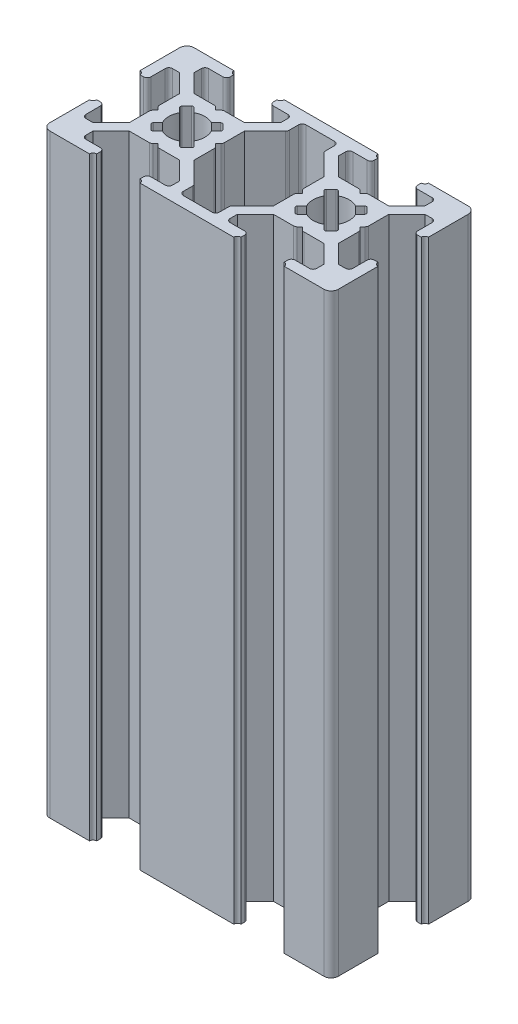
SolidWorks part; units mm, degrees
ref_plane "Front Plane" through (0, 0, 0) normal (0, 0, 1) x (1, 0, 0)
ref_plane "Top Plane" through (0, 0, 0) normal (0, 1, 0) x (1, 0, 0)
ref_plane "Right Plane" through (0, 0, 0) normal (1, 0, 0) x (0, 0, -1)
sketch "Sketch2" plane through (0, 0, 0) normal (0, 1, 0) x (1, 0, 0)
  line L0 (0, 13) -> (1.5, 13)
  line L1 (0, 0) -> (40, 0)
  line L2 (0, 0) -> (0, 20)
  line L3 (0, 20) -> (40, 20)
  line L4 (40, 0) -> (40, 20)
  line L9 (5.5, 6.5) -> (3, 4)
  line L10 (3, 4) -> (1.5, 4)
  line L11 (1.5, 4) -> (1.5, 7)
  line L12 (1.5, 7) -> (0, 7)
  line L13 (0, 7) -> (0, 13)
  line L14 (1.5, 13) -> (1.5, 16)
  line L15 (1.5, 16) -> (3, 16)
  line L16 (3, 16) -> (5.5, 13.5)
  line L17 (5.5, 10.5) -> (6, 10)
  line L18 (6, 10) -> (5.5, 9.5)
  line L19 (5.5, 9.5) -> (5.5, 10.5)
  line L20 (20, 20) -> (20, 0) construction
  line L31 (7, 18.5) -> (7, 20)
  line L32 (7, 18.5) -> (4, 18.5)
  line L33 (4, 18.5) -> (4, 17)
  line L34 (4, 17) -> (6.5, 14.5)
  line L38 (16, 18.5) -> (13, 18.5)
  line L39 (13, 18.5) -> (13, 20)
  line L40 (7, 20) -> (13, 20)
  line L41 (16, 18.5) -> (16, 17)
  line L42 (16, 17) -> (13.5, 14.5)
  line L53 (0, 10) -> (40, 10) construction
  line L89 (17.5, 18.5) -> (22.5, 18.5)
  line L90 (22.5, 18.5) -> (22.5, 16.5)
  line L91 (22.5, 16.5) -> (25.5, 13.5)
  line L92 (25.5, 13.5) -> (25.5, 6.5)
  line L93 (25.5, 6.5) -> (22.5, 3.5)
  line L94 (22.5, 3.5) -> (22.5, 1.5)
  line L95 (22.5, 1.5) -> (17.5, 1.5)
  line L96 (17.5, 1.5) -> (17.5, 3.5)
  line L97 (17.5, 3.5) -> (14.5, 6.5)
  line L98 (14.5, 6.5) -> (14.5, 13.5)
  line L99 (14.5, 13.5) -> (17.5, 16.5)
  line L100 (17.5, 16.5) -> (17.5, 18.5)
  line L102 (5.5, 13.5) -> (5.5, 10)
  line L103 (5.5, 10) -> (5.5, 6.5)
  line L104 (13.5, 14.5) -> (10, 14.5)
  line L105 (10, 14.5) -> (6.5, 14.5)
  line L106 (14.5, 10.5) -> (14.5, 9.5)
  line L107 (14.5, 9.5) -> (14, 10)
  line L108 (14, 10) -> (14.5, 10.5)
  line L109 (7, 18.5) -> (13, 18.5) construction
  line L110 (9.5, 14.5) -> (10.5, 14.5)
  line L111 (10.5, 14.5) -> (10, 14)
  line L112 (10, 14) -> (9.5, 14.5)
  line L113 (10.5, 5.5) -> (10, 6)
  line L114 (9.5, 5.5) -> (10.5, 5.5)
  line L115 (10, 6) -> (9.5, 5.5)
  line L116 (13.5, 5.5) -> (10, 5.5)
  line L117 (16, 3) -> (13.5, 5.5)
  line L118 (16, 1.5) -> (16, 3)
  line L119 (16, 1.5) -> (13, 1.5)
  line L120 (13, 1.5) -> (13, 0)
  line L121 (7, 0) -> (13, 0)
  line L122 (7, 1.5) -> (7, 0)
  line L123 (7, 1.5) -> (4, 1.5)
  line L124 (4, 1.5) -> (4, 3)
  line L125 (4, 3) -> (6.5, 5.5)
  line L126 (10, 5.5) -> (6.5, 5.5)
  line L127 (30.5, 5.5) -> (29.5, 5.5)
  line L128 (30, 6) -> (30.5, 5.5)
  line L129 (29.5, 5.5) -> (30, 6)
  line L130 (24, 3) -> (26.5, 5.5)
  line L131 (24, 1.5) -> (24, 3)
  line L132 (24, 1.5) -> (27, 1.5)
  line L133 (27, 1.5) -> (27, 0)
  line L134 (33, 0) -> (27, 0)
  line L135 (33, 1.5) -> (33, 0)
  line L136 (33, 1.5) -> (36, 1.5)
  line L137 (36, 1.5) -> (36, 3)
  line L138 (36, 3) -> (33.5, 5.5)
  line L139 (30, 5.5) -> (33.5, 5.5)
  line L140 (26.5, 5.5) -> (30, 5.5)
  line L141 (34, 10) -> (34.5, 9.5)
  line L142 (34.5, 10.5) -> (34, 10)
  line L143 (34.5, 9.5) -> (34.5, 10.5)
  line L144 (34.5, 13.5) -> (34.5, 10)
  line L145 (37, 16) -> (34.5, 13.5)
  line L146 (38.5, 16) -> (37, 16)
  line L147 (38.5, 13) -> (38.5, 16)
  line L148 (40, 13) -> (38.5, 13)
  line L149 (40, 7) -> (40, 13)
  line L150 (38.5, 7) -> (40, 7)
  line L151 (38.5, 4) -> (38.5, 7)
  line L152 (37, 4) -> (38.5, 4)
  line L153 (34.5, 6.5) -> (37, 4)
  line L154 (34.5, 10) -> (34.5, 6.5)
  line L155 (29.5, 14.5) -> (30, 14)
  line L156 (30.5, 14.5) -> (29.5, 14.5)
  line L157 (30, 14) -> (30.5, 14.5)
  line L158 (26.5, 14.5) -> (30, 14.5)
  line L159 (24, 17) -> (26.5, 14.5)
  line L160 (24, 18.5) -> (24, 17)
  line L161 (24, 18.5) -> (27, 18.5)
  line L162 (27, 18.5) -> (27, 20)
  line L163 (33, 20) -> (27, 20)
  line L164 (33, 18.5) -> (33, 20)
  line L165 (33, 18.5) -> (36, 18.5)
  line L166 (36, 18.5) -> (36, 17)
  line L167 (36, 17) -> (33.5, 14.5)
  line L168 (30, 14.5) -> (33.5, 14.5)
  line L169 (13.5, 14.5) -> (14.5, 13.5) construction
  line L170 (5.5, 6.5) -> (6.5, 5.5) construction
  line L171 (6.5, 14.5) -> (5.5, 13.5) construction
  line L172 (14.5, 6.5) -> (13.5, 5.5) construction
  line L173 (14.5, 10.5) -> (10.5, 14.5) construction
  line L174 (10.5, 5.5) -> (14.5, 9.5) construction
  line L175 (9.5, 5.5) -> (5.5, 9.5) construction
  line L176 (5.5, 10.5) -> (9.5, 14.5) construction
  line L177 (12, 13) -> (13, 12)
  line L178 (13, 12) -> (8, 7)
  line L179 (8, 7) -> (7, 8)
  line L180 (7, 8) -> (12, 13)
  line L181 (8, 13) -> (13, 8)
  line L182 (13, 8) -> (12, 7)
  line L183 (12, 7) -> (7, 12)
  line L184 (7, 12) -> (8, 13)
  line L185 (28, 7) -> (33, 12)
  line L186 (27, 8) -> (28, 7)
  line L187 (32, 13) -> (27, 8)
  line L188 (33, 12) -> (32, 13)
  line L189 (32, 7) -> (33, 8)
  line L190 (27, 12) -> (32, 7)
  line L191 (28, 13) -> (27, 12)
  line L192 (33, 8) -> (28, 13)
  line L193 (13.5, 20) -> (13, 20)
  line L194 (13, 19.5) -> (13, 20)
  line L195 (6.5, 20) -> (7, 20)
  line L196 (0, 13.5) -> (0, 13)
  line L197 (0.25, 7) -> (0, 7)
  line L198 (7, 19.5) -> (7, 20)
  line L199 (0.25, 7) -> (0, 7)
  line L200 (33, 19.5) -> (33, 20)
  line L201 (33.5, 20) -> (33, 20)
  line L202 (27, 19.5) -> (27, 20)
  line L203 (26.5, 20) -> (27, 20)
  line L204 (33, 0.5) -> (33, 0)
  line L205 (33.5, 0) -> (33, 0)
  line L206 (27, 0.5) -> (27, 0)
  line L207 (26.5, 0) -> (27, 0)
  line L208 (13, 0.5) -> (13, 0)
  line L209 (13.5, 0) -> (13, 0)
  line L210 (7, 0.5) -> (7, 0)
  line L211 (6.5, 0) -> (7, 0)
  line L212 (0.5, 13) -> (0, 13)
  line L213 (0, 6.75) -> (0, 7)
  line L214 (0, 6.75) -> (0, 7)
  line L215 (0, 7) -> (0.25, 7)
  line L216 (0, 6.5) -> (0, 7)
  line L217 (0, 7) -> (0.5, 7)
  line L218 (39.5, 13) -> (40, 13)
  line L219 (40, 13.5) -> (40, 13)
  line L220 (40, 6.5) -> (40, 7)
  line L221 (40, 7) -> (39.5, 7)
  line L222 (25.5, 9.5) -> (26, 10)
  line L223 (25.5, 10.5) -> (25.5, 9.5)
  line L224 (26, 10) -> (25.5, 10.5)
  circle A0 centre (10, 10) radius 2.5
  circle A1 centre (30, 10) radius 2.5
  arc A2 (13.5, 20) -> (13, 19.5) centre (13, 20) cw
  arc A3 (7, 19.5) -> (6.5, 20) centre (7, 20) cw
  arc A4 (0.5, 13) -> (0, 13.5) centre (0, 13) ccw
  arc A5 (0.5, 7) -> (0, 6.5) centre (0, 7) cw
  arc A6 (33, 19.5) -> (33.5, 20) centre (33, 20) ccw
  arc A7 (26.5, 20) -> (27, 19.5) centre (27, 20) ccw
  arc A8 (33, 0.5) -> (33.5, 0) centre (33, 0) cw
  arc A9 (26.5, 0) -> (27, 0.5) centre (27, 0) cw
  arc A10 (13.5, 0) -> (13, 0.5) centre (13, 0) ccw
  arc A11 (7, 0.5) -> (6.5, 0) centre (7, 0) ccw
  arc A12 (39.5, 13) -> (40, 13.5) centre (40, 13) cw
  arc A13 (39.5, 7) -> (40, 6.5) centre (40, 7) ccw
  point P19 (20, 10)
  point P103 (14.5, 10)
  dimension "D31" = 5
  dimension "D32" = 0.5
  dimension "D33" = 0.5
  dimension "D34" = 0.5
  dimension "D35" = 0.5
  dimension "D1" = 40
  dimension "D2" = 20
  dimension "D3" = 7
  dimension "D4" = 7
  dimension "D5" = 1.5
  dimension "D6" = 1.5
  dimension "D7" = 3.5
  dimension "D8" = 1.5
  dimension "D9" = 1.5
  dimension "D10" = 3
  dimension "D11" = 3
  dimension "D12" = 3.5
  dimension "D13" = 0.5
  dimension "D14" = 0.5
  dimension "D15" = 7
  dimension "D16" = 6
  dimension "D17" = 1.5
  dimension "D18" = 1.5
  dimension "D19" = 3
  dimension "D20" = 3
  dimension "D21" = 0.5
  dimension "D22" = 1.5
  dimension "D23" = 5.5
  dimension "D24" = 0.5
  dimension "D25" = 0.5
  dimension "D26" = 1.5
  dimension "D27" = 1.5
  dimension "D28" = 2
  dimension "D29" = 2
  dimension "D30" = 0.5
extrude "Boss-Extrude1" add sketch "Sketch2" along normal blind 82.5 contours L168 L157 L155 L158 L159 L160 L161 L162 L3 L39 L38 L41 L42 L104 L111 L112 L105 L34 L33 L32 L31 L2 L0 L14 L15 L16 L102 L17 L18 L103 L9 L10 L11 L12 L1 L122 L123 L124 L125 L126 L115 L113 L116 L117 L118 L119 L120 L133
fillet "Fillet1" radius 1 4 edges at (40, 41.25, -20) (40, 41.25, 0) (0, 41.25, 0) (0, 41.25, -20)
fillet "Fillet2" radius 0.5 6 edges at (13, 41.25, -18.5) (16, 41.25, -18.5) (10.5, 41.25, -14.5) (9.5, 41.25, -14.5) (4, 41.25, -18.5) (7, 41.25, -18.5)
fillet "Fillet3" radius 0.25 8 edges at (8, 41.25, -7) (7, 41.25, -8) (12, 41.25, -7) (13, 41.25, -8) (13, 41.25, -12) (12, 41.25, -13) (7, 41.25, -12) (8, 41.25, -13)
fillet "Fillet5" radius 0.25 8 edges at (27, 41.25, -8) (28, 41.25, -7) (32, 41.25, -7) (33, 41.25, -8) (33, 41.25, -12) (32, 41.25, -13) (27, 41.25, -12) (28, 41.25, -13)
fillet "Fillet6" radius 0.5 30 edges at (36, 41.25, -18.5) (33, 41.25, -18.5) (30.5, 41.25, -14.5) (29.5, 41.25, -14.5) (24, 41.25, -18.5) (27, 41.25, -18.5) (38.5, 41.25, -4) (38.5, 41.25, -7) (34.5, 41.25, -9.5) (34.5, 41.25, -10.5) (38.5, 41.25, -16) (38.5, 41.25, -13) (24, 41.25, -1.5) (27, 41.25, -1.5) (29.5, 41.25, -5.5) (30.5, 41.25, -5.5) (36, 41.25, -1.5) (33, 41.25, -1.5) (4, 41.25, -1.5) (7, 41.25, -1.5) (9.5, 41.25, -5.5) (10.5, 41.25, -5.5) (16, 41.25, -1.5) (13, 41.25, -1.5) (5.5, 41.25, -10.5) (5.5, 41.25, -9.5) (1.5, 41.25, -4) (1.5, 41.25, -7) (1.5, 41.25, -16) (1.5, 41.25, -13)
fillet "Fillet7" radius 0.5 8 edges at (22.5, 41.25, -3.5) (22.5, 41.25, -1.5) (17.5, 41.25, -3.5) (17.5, 41.25, -1.5) (17.5, 41.25, -16.5) (22.5, 41.25, -16.5) (22.5, 41.25, -18.5) (17.5, 41.25, -18.5)
fillet "Fillet8" radius 0.5 4 edges at (25.5, 41.25, -9.5) (25.5, 41.25, -10.5) (14.5, 41.25, -9.5) (14.5, 41.25, -10.5)
